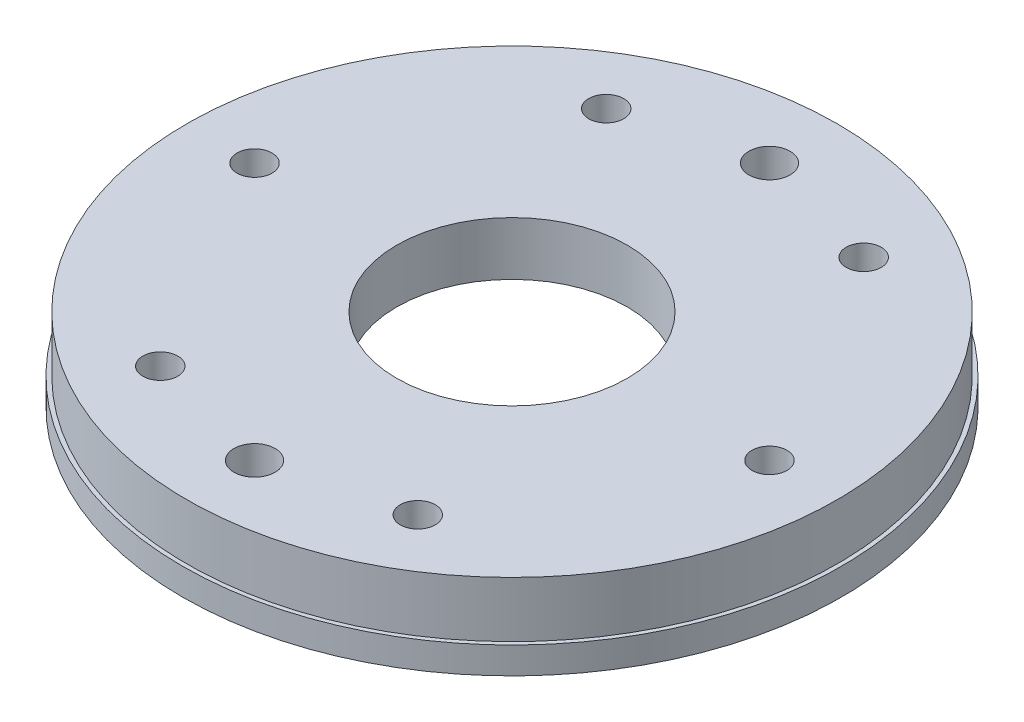
SolidWorks part; units mm, degrees
ref_plane "Piano frontale" through (0, 0, 0) normal (0, 0, 1) x (1, 0, 0)
ref_plane "Piano superiore" through (0, 0, 0) normal (0, 1, 0) x (1, 0, 0)
ref_plane "Piano destro" through (0, 0, 0) normal (1, 0, 0) x (0, 0, -1)
sketch "Schizzo1" plane through (0, 0, 0) normal (0, 0, 1) x (1, 0, 0)
  line L0 (0, 0) -> (0, 57.7061) construction
  line L1 (0, 0) -> (80, 0)
  line L2 (80, 0) -> (80, 6.5)
  line L3 (80, 6.5) -> (79, 6.5)
  line L4 (79, 6.5) -> (79, 20)
  line L5 (79, 20) -> (0, 20)
  line L6 (0, 0) -> (0, 20)
  dimension "D1" = 160
  dimension "D2" = 6.5
  dimension "D3" = 13.5
  dimension "D4" = 158
revolve "Rivoluzione1" add sketch "Schizzo1" angle 360 about L0
sketch "Schizzo2" plane through (0, 0, 0) normal (0, -1, 0) x (1, 0, 0)
  circle A0 centre (0, 0) radius 28
  dimension "D1" = 56
extrude "Taglio-Estrusione1" cut sketch "Schizzo2" against normal through all
hole_wizard "M10 Foro filettato profondo1" positions "Schizzo4" profile "Schizzo3" tap size "M10" standard "Celli-ISO"
sketch "Schizzo4" plane through (0, 0, 0) normal (0, -1, 0) x (1, 0, 0)
  line L0 (0, 0) -> (62.5, 0) construction
  circle A0 centre (0, 0) radius 62.5 construction
  point P0 (62.5, 0)
  dimension "D1" = 125
sketch "Schizzo3" plane through (62.5, 0, 0) normal (1, 0, 0) x (0, 0, -1)
  line L0 (0, 0) -> (0, 27.5537)
  line L1 (0, 27.5537) -> (4.25, 25)
  line L2 (4.25, 25) -> (4.25, 0)
  line L5 (4.25, 0) -> (0, 0)
  line L10 (0, 27.5537) -> (-4.25, 25) construction
  line L11 (0, -6.35) -> (0, 107.95) construction
  dimension "Tap Drill Dia." = 8.5
  dimension "Tap Drill Depth" = 25
  dimension "Drill Angle" = 118
cosmetic thread "Filettatura del foro1" parameters "D1"=21, "D2"=10
pattern_circular "RipetizioneCircolare1" count 6 over 360 about axis through (0, 0, 0) along (0, 1, 0) of "M10 Foro filettato profondo1"
sketch "Schizzo5" plane through (0, 0, 0) normal (0, -1, 0) x (1, 0, 0)
  line L0 (0, 62.5) -> (0, -62.5) construction
  circle A0 centre (0, 0) radius 62.5 construction
  circle A1 centre (0, 62.5) radius 5
  circle A2 centre (0, -62.5) radius 5
  dimension "D1" = 10
extrude "Taglio-Estrusione2" cut sketch "Schizzo5" against normal through all
sketch "Schizzo6" plane through (0, 0, 0) normal (0, -1, 0) x (1, 0, 0)
  circle A0 centre (0, 0) radius 40
  dimension "D1" = 80
extrude "Taglio-Estrusione3" cut sketch "Schizzo6" against normal blind 7
